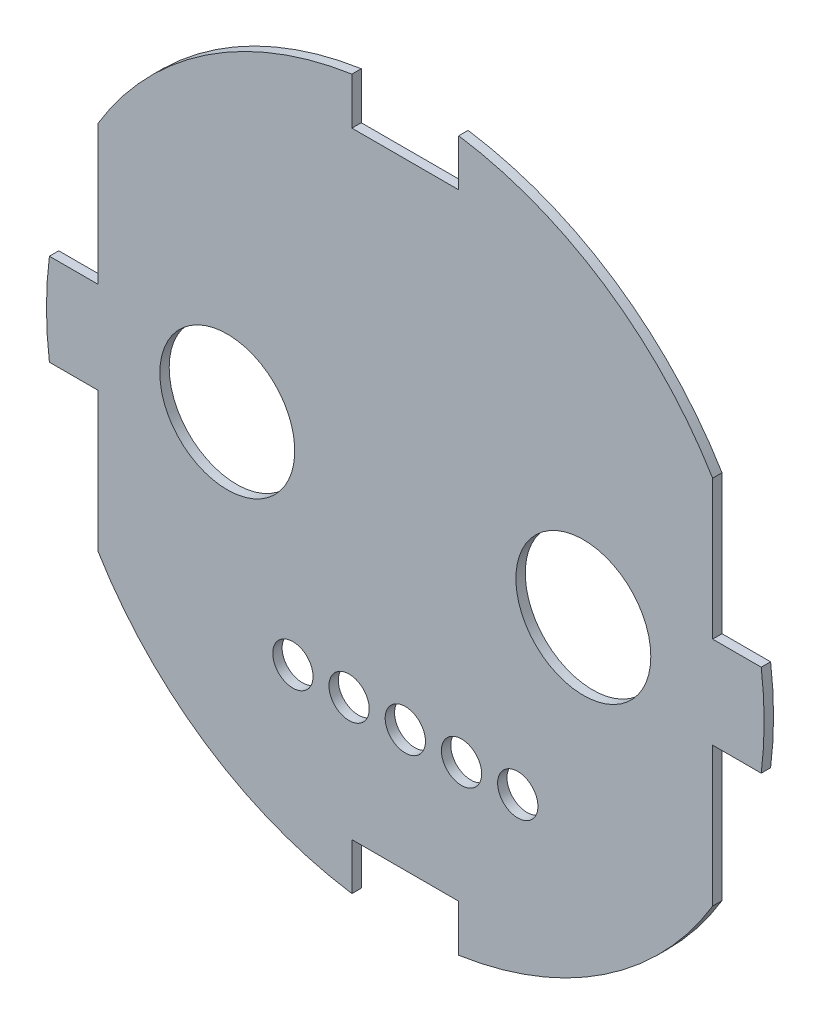
SolidWorks part; units mm, degrees
ref_plane "Ön Düzlem" through (0, 0, 0) normal (0, 0, 1) x (1, 0, 0)
ref_plane "Üst Düzlem" through (0, 0, 0) normal (0, 1, 0) x (1, 0, 0)
ref_plane "Sağ Düzlem" through (0, 0, 0) normal (1, 0, 0) x (0, 0, -1)
sketch "Çizim1" plane through (0, 0, 0) normal (0, 0, 1) x (1, 0, 0)
  line L0 (0, 72.5644) -> (0, -45.3079) construction
  line L1 (71.2056, 0) -> (-77.0314, 0) construction
  line L2 (-19.2979, 2.8) -> (-16.75, 2.8)
  line L3 (-16.75, 2.8) -> (-16.75, 9.9844)
  line L4 (-2.5, 16.7891) -> (2.5, 16.7891)
  line L5 (2.5, 16.7891) -> (2.5, 19.3391)
  line L6 (-2.5, 16.7891) -> (-2.5, 19.3391)
  line L7 (-2.5, -16.7891) -> (-2.5, -19.3391)
  line L8 (-2.5, -16.7891) -> (2.5, -16.7891)
  line L9 (2.5, -16.7891) -> (2.5, -19.3391)
  line L10 (-19.2979, -2.8) -> (-16.75, -2.8)
  line L11 (-16.75, -2.8) -> (-16.75, -9.9844)
  line L12 (19.2979, 2.8) -> (16.75, 2.8)
  line L13 (16.75, 2.8) -> (16.75, 9.9844)
  line L14 (19.2979, -2.8) -> (16.75, -2.8)
  line L15 (16.75, -2.8) -> (16.75, -9.9844)
  arc A0 (-2.5, 19.3391) -> (-16.75, 9.9844) centre (0, 0) ccw
  circle A1 centre (9.5, 0) radius 3.25
  circle A2 centre (0, -9.9391) radius 0.725
  circle A3 centre (-9.5, 0) radius 3.25
  circle A4 centre (3, -9.9391) radius 0.725
  circle A5 centre (6, -9.9391) radius 0.725
  circle A6 centre (-3, -9.9391) radius 0.725
  circle A7 centre (-6, -9.9391) radius 0.725
  arc A8 (2.5, -19.3391) -> (16.75, -9.9844) centre (0, 0) ccw
  arc A9 (19.2979, -2.8) -> (19.2979, 2.8) centre (0, 0) ccw
  arc A10 (16.75, 9.9844) -> (2.5, 19.3391) centre (0, 0) ccw
  arc A11 (-19.2979, 2.8) -> (-19.2979, -2.8) centre (0, 0) ccw
  arc A12 (-16.75, -9.9844) -> (-2.5, -19.3391) centre (0, 0) ccw
  point P19 (0, 16.7891)
extrude "Yükseklik-Ekstrüzyon3" add sketch "Çizim1" along normal blind 0.5
sketch "Çizim2" plane through (0, 0, 0.5) normal (0, 0, 1) x (1, 0, 0)
  line L0 (0, 0) -> (0, 13.1789) construction
  line L1 (0, 0) -> (17.2051, 0) construction
  line L2 (-19.2979, 2.8) -> (-16.75, 2.8)
  line L3 (-16.75, 2.8) -> (-16.75, 9.9844)
  line L4 (-2.5, 16.7891) -> (2.5, 16.7891)
  line L5 (2.5, 16.7891) -> (2.5, 19.3391)
  line L6 (-2.5, 16.7891) -> (-2.5, 19.3391)
  line L7 (-2.5, -16.7891) -> (-2.5, -19.3391)
  line L8 (-2.5, -16.7891) -> (2.5, -16.7891)
  line L9 (2.5, -16.7891) -> (2.5, -19.3391)
  line L10 (-19.2979, -2.8) -> (-16.75, -2.8)
  line L11 (-16.75, -2.8) -> (-16.75, -9.9844)
  line L12 (19.2979, 2.8) -> (16.75, 2.8)
  line L13 (16.75, 2.8) -> (16.75, 9.9844)
  line L14 (19.2979, -2.8) -> (16.75, -2.8)
  line L15 (16.75, -2.8) -> (16.75, -9.9844)
  arc A0 (-2.5, 19.3391) -> (-16.75, 9.9844) centre (0, 0) ccw
  circle A1 centre (9.5, 0) radius 3.25
  circle A2 centre (0, -9.9391) radius 0.725
  circle A3 centre (-9.5, 0) radius 3.25
  circle A4 centre (3, -9.9391) radius 0.725
  circle A5 centre (6, -9.9391) radius 0.725
  circle A6 centre (-3, -9.9391) radius 0.725
  circle A7 centre (-6, -9.9391) radius 0.725
  arc A8 (2.5, -19.3391) -> (16.75, -9.9844) centre (0, 0) ccw
  arc A9 (19.2979, -2.8) -> (19.2979, 2.8) centre (0, 0) ccw
  arc A10 (16.75, 9.9844) -> (2.5, 19.3391) centre (0, 0) ccw
  arc A11 (-19.2979, 2.8) -> (-19.2979, -2.8) centre (0, 0) ccw
  arc A12 (-16.75, -9.9844) -> (-2.5, -19.3391) centre (0, 0) ccw
  point P19 (0, 16.7891)
extrude "Kes-Ekstrüzyon-İnce1" cut sketch "Çizim2" against normal blind 0.5 thin thin type mid plane wall 0.7
